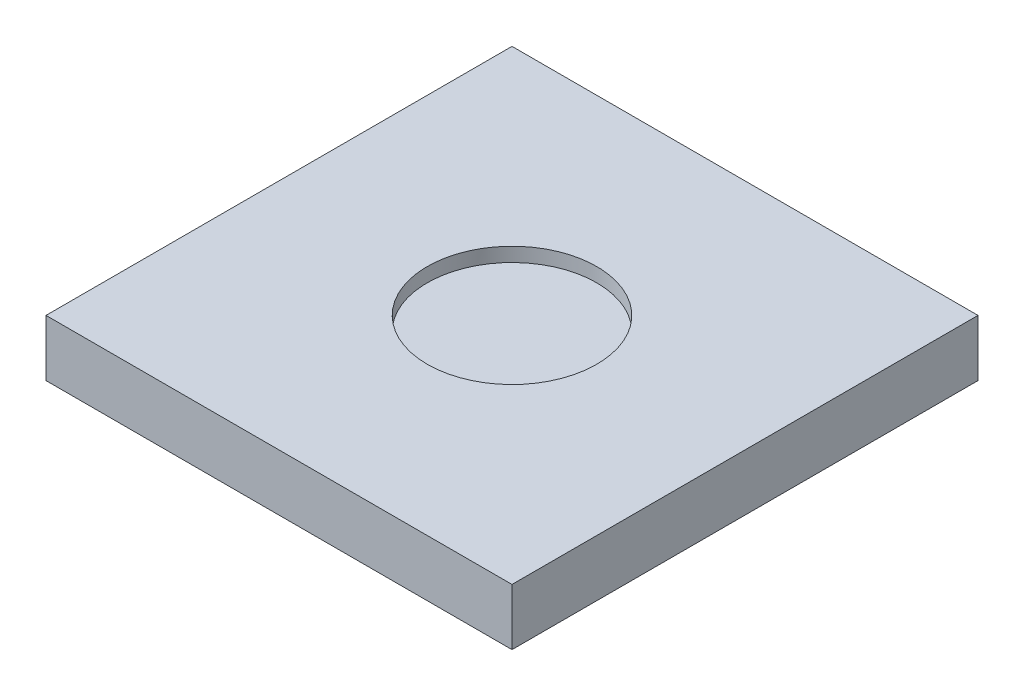
SolidWorks part; units mm, degrees
ref_plane "Front Plane" through (0, 0, 0) normal (0, 0, 1) x (1, 0, 0)
ref_plane "Top Plane" through (0, 0, 0) normal (0, 1, 0) x (1, 0, 0)
ref_plane "Right Plane" through (0, 0, 0) normal (1, 0, 0) x (0, 0, -1)
sketch "Sketch1" plane through (0, 0, 0) normal (0, 1, 0) x (1, 0, 0)
  line L1 (-15.5, -15.5) -> (15.5, -15.5)
  line L2 (-15.5, -15.5) -> (-15.5, 15.5)
  line L3 (-15.5, 15.5) -> (15.5, 15.5)
  line L4 (15.5, -15.5) -> (15.5, 15.5)
  line L5 (-15.5, -15.5) -> (15.5, 15.5) construction
  line L6 (-15.5, 15.5) -> (15.5, -15.5) construction
  line L7 (-16.5, -16.5) -> (16.5, -16.5)
  line L8 (-16.5, -16.5) -> (-16.5, 16.5)
  line L9 (-16.5, 16.5) -> (16.5, 16.5)
  line L10 (16.5, -16.5) -> (16.5, 16.5)
  line L11 (-16.5, -16.5) -> (16.5, 16.5) construction
  line L12 (-16.5, 16.5) -> (16.5, -16.5) construction
  point P0 (0, 0)
  point P6 (0, 0)
  dimension "D1" = 31
  dimension "D2" = 31
  dimension "D3" = 1
  dimension "D4" = 1
extrude "Boss-Extrude1" add sketch "Sketch1" along normal blind 3
sketch "Sketch2" plane through (0, 3, 0) normal (0, 1, 0) x (1, 0, 0)
  line L1 (-16.5, -16.5) -> (16.5, -16.5)
  line L2 (-16.5, -16.5) -> (-16.5, 16.5)
  line L3 (-16.5, 16.5) -> (16.5, 16.5)
  line L4 (16.5, -16.5) -> (16.5, 16.5)
  line L5 (-16.5, -16.5) -> (16.5, 16.5) construction
  line L6 (-16.5, 16.5) -> (16.5, -16.5) construction
  point P0 (0, 0)
extrude "Boss-Extrude2" add sketch "Sketch2" along normal blind 1
sketch "Sketch3" plane through (0, 4, 0) normal (0, 1, 0) x (1, 0, 0)
  circle A0 centre (0, 0) radius 6
  dimension "D1" = 12
extrude "Cut-Extrude1" cut sketch "Sketch3" against normal through all
sketch "Sketch4" plane through (0, 3, 0) normal (0, -1, 0) x (1, 0, 0)
  circle A0 centre (0, 0) radius 8
  dimension "D1" = 16
extrude "Boss-Extrude3" add sketch "Sketch4" along normal blind 1
